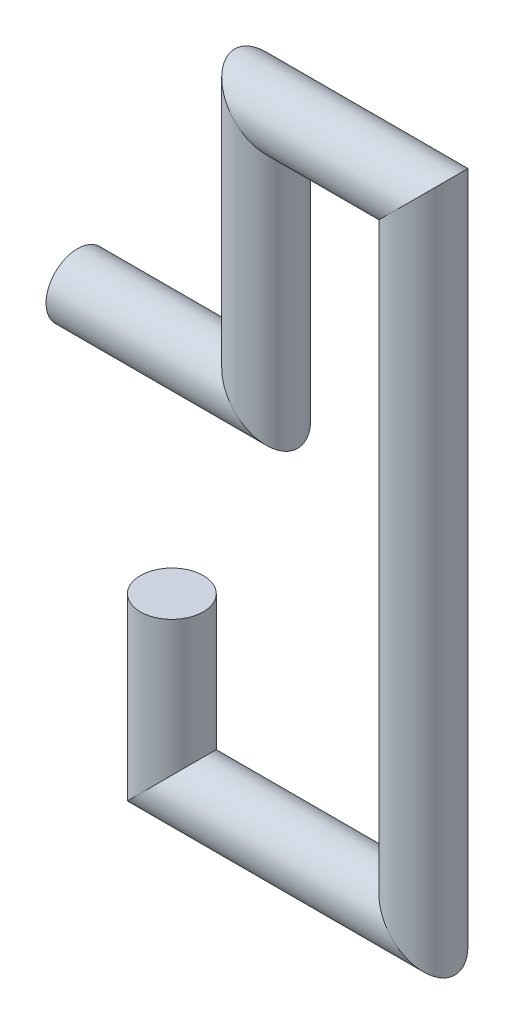
SolidWorks part; units mm, degrees
ref_plane "정면" through (0, 0, 0) normal (0, 0, 1) x (1, 0, 0)
ref_plane "윗면" through (0, 0, 0) normal (0, 1, 0) x (1, 0, 0)
ref_plane "우측면" through (0, 0, 0) normal (1, 0, 0) x (0, 0, -1)
sketch "스케치1" plane through (0, 0, 0) normal (0, 0, 1) x (1, 0, 0)
  line L0 (0, 0) -> (60, 0)
  line L1 (60, 0) -> (60, 80)
  line L2 (60, 80) -> (110, 80)
  line L3 (110, 80) -> (110, -120)
  line L4 (110, -120) -> (30, -120)
  line L5 (30, -120) -> (30, -70)
  dimension "D1" = 60
  dimension "D2" = 80
  dimension "D3" = 50
  dimension "D4" = 200
  dimension "D5" = 80
  dimension "D6" = 50
sketch "스케치2" plane through (0, 0, 0) normal (1, 0, 0) x (0, 0, -1)
  circle A0 centre (0, 0) radius 10
  dimension "D1" = 20
sweep "스윕1" add profiles "스케치2" path "스케치1"
